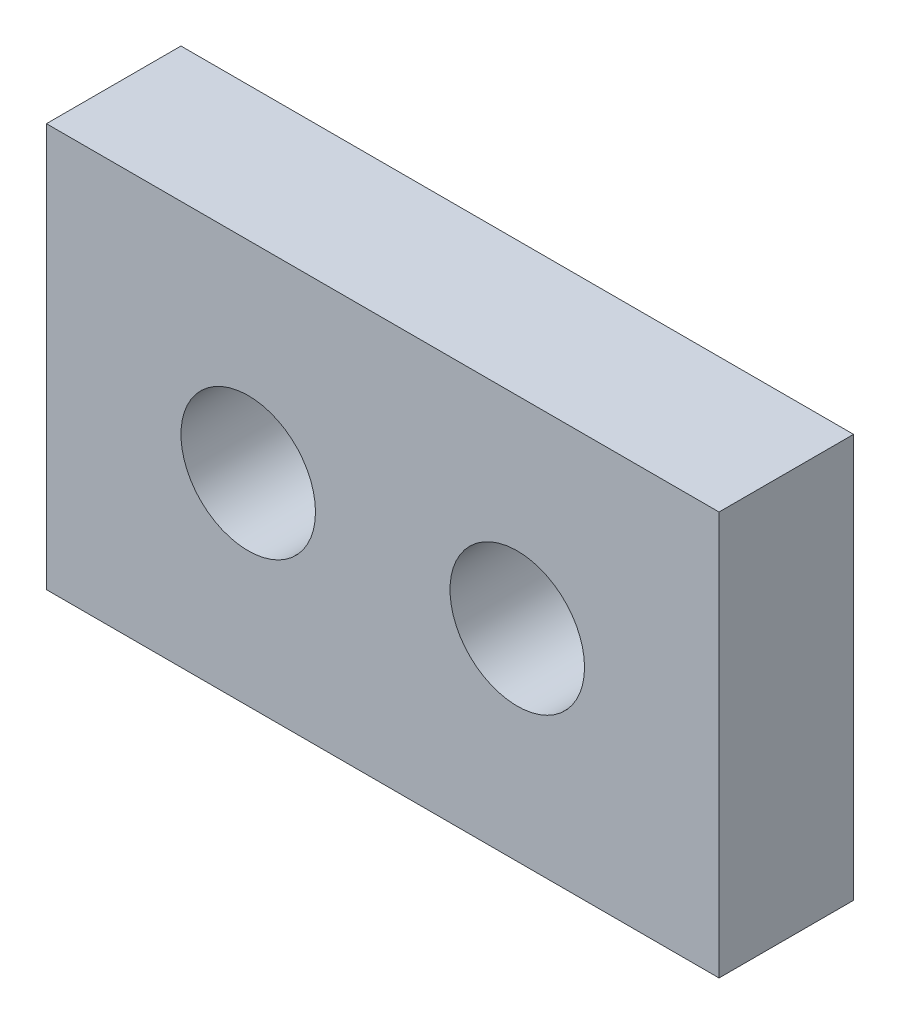
SolidWorks part; units mm, degrees
ref_plane "Front" through (0, 0, 0) normal (0, 0, 1) x (1, 0, 0)
ref_plane "Top" through (0, 0, 0) normal (0, 1, 0) x (1, 0, 0)
ref_plane "Right" through (0, 0, 0) normal (1, 0, 0) x (0, 0, -1)
sketch "Sketch1" plane through (0, 0, 0) normal (0, 0, 1) x (1, 0, 0)
  line L1 (0, 0) -> (50, 0)
  line L2 (0, 0) -> (0, 30)
  line L3 (0, 30) -> (50, 30)
  line L4 (50, 0) -> (50, 30)
  dimension "D1" = 50
  dimension "D2" = 30
extrude "Boss-Extrude1" add sketch "Sketch1" along normal blind 10
sketch "Sketch2" plane through (0, 0, 10) normal (0, 0, 1) x (1, 0, 0)
  line L0 (0, 15) -> (50, 15) construction
  line L1 (0, 30) -> (0, 0) construction
  line L2 (50, 0) -> (50, 30) construction
  line L3 (25, 30) -> (25, -3.1769) construction
  line L4 (50, 30) -> (0, 30) construction
  circle A0 centre (15, 15) radius 5
  circle A1 centre (35, 15) radius 5
  dimension "D1" = 10
  dimension "D2" = 15
extrude "Cut-Extrude1" cut sketch "Sketch2" against normal through all
